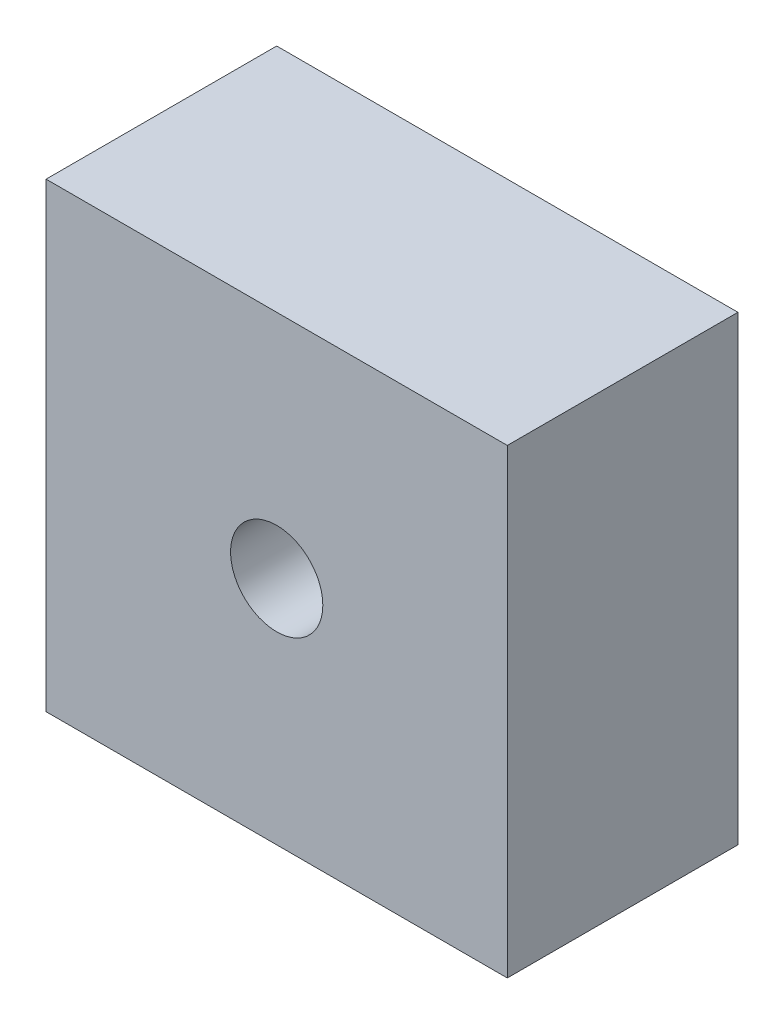
SolidWorks part; units mm, degrees
material "ASTM A36 Steel"
ref_plane "Front Plane" through (0, 0, 0) normal (0, 0, 1) x (1, 0, 0)
ref_plane "Top Plane" through (0, 0, 0) normal (0, 1, 0) x (1, 0, 0)
ref_plane "Right Plane" through (0, 0, 0) normal (1, 0, 0) x (0, 0, -1)
sketch "Sketch1" plane through (0, 0, 0) normal (0, 0, 1) x (1, 0, 0)
  line L1 (63.5, -63.5) -> (-63.5, -63.5)
  line L2 (63.5, -63.5) -> (63.5, 63.5)
  line L3 (63.5, 63.5) -> (-63.5, 63.5)
  line L4 (-63.5, -63.5) -> (-63.5, 63.5)
  line L5 (63.5, -63.5) -> (-63.5, 63.5) construction
  line L6 (63.5, 63.5) -> (-63.5, -63.5) construction
  point P0 (0, 0)
  dimension "D1" = 127
  dimension "D2" = 127
extrude "Boss-Extrude1" add sketch "Sketch1" against normal blind 63.5
sketch "Sketch2" plane through (0, 0, 0) normal (0, 0, 1) x (1, 0, 0)
  circle A0 centre (0, 0) radius 12.7
  dimension "D1" = 25.4
extrude "Cut-Extrude1" cut sketch "Sketch2" against normal blind 63.5
